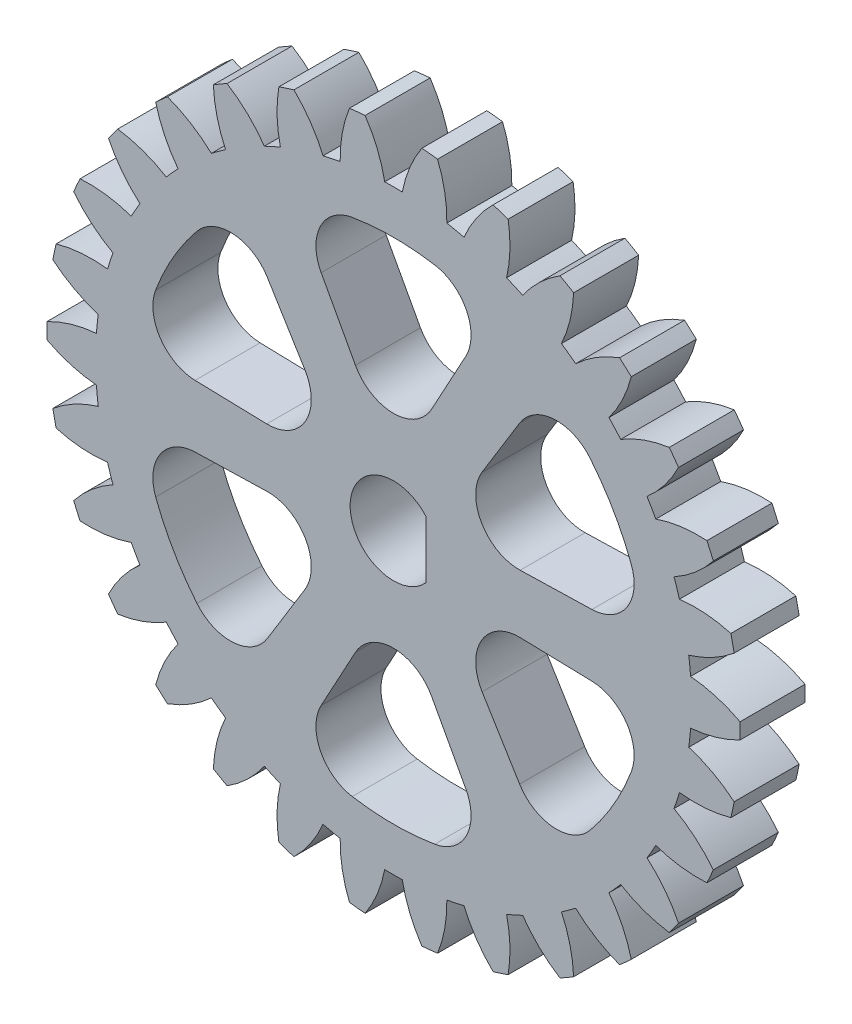
SolidWorks part; units mm, degrees
ref_plane "Front Plane" through (0, 0, 0) normal (0, 0, 1) x (1, 0, 0)
ref_plane "Top Plane" through (0, 0, 0) normal (0, 1, 0) x (1, 0, 0)
ref_plane "Right Plane" through (0, 0, 0) normal (1, 0, 0) x (0, 0, -1)
sketch "Sketch1" plane through (0, 0, 0) normal (0, 0, 1) x (1, 0, 0)
  circle A0 centre (0, 0) radius 16
  dimension "addendumDiameter" = 32
extrude "Boss-Extrude1" add sketch "Sketch1" along normal blind 3
sketch "Sketch3" plane through (0, 0, 3) normal (0, 0, 1) x (1, 0, 0)
  line L0 (0, 0) -> (-3.2905, 31.3074) construction
  line L1 (0, 0) -> (0, 28.4418) construction
  line L2 (-0.7847, 14.9795) -> (-1.5658, 14.8974) construction
  circle A0 centre (0, 0) radius 14.0954 construction
  circle A1 centre (0, 0) radius 15 construction
  circle A2 centre (0, 0) radius 13.75 construction
  arc A3 (0.4053, 13.744) -> (-0.4053, 13.744) centre (0, 0) ccw
  arc A4 (1.31, 15.9463) -> (-1.31, 15.9463) centre (0, 0) ccw
  circle A5 centre (0, 0) radius 16 construction
  arc A6 (-1.31, 15.9463) -> (-0.4053, 13.744) centre (-6.2972, 12.6105) cw
  arc A7 (1.31, 15.9463) -> (0.4053, 13.744) centre (6.2972, 12.6105) ccw
  point P16 (0, 13.75)
  dimension "D1" = 27.5
  dimension "D2" = 28.1908
  dimension "D3" = 30
  dimension "D5" = 6
  dimension "D6" = 6
  dimension "D4" = 6
  dimension "D7" = 0.7854
extrude "Cut-Extrude1" cut sketch "Sketch3" against normal through all
pattern_circular "CirPattern1" count 30 over 360 about axis through (0, 0, 0) along (0, 0, 1) of "Cut-Extrude1"
sketch "Sketch4" plane through (0, 0, 3) normal (0, 0, 1) x (1, 0, 0)
  line L0 (0, 0) -> (0, 11.7308) construction
  line L1 (0, 2.5) -> (-4.5201, 10.825)
  line L3 (4.5201, 10.825) -> (0, 2.5)
  arc A0 (-4.5201, 10.825) -> (4.5201, 10.825) centre (0, 0) cw
  point P7 (0, 11.7308)
  dimension "D1" = 2.5
  dimension "D2" = 9.2308
  dimension "D3" = 57
extrude "Cut-Extrude2" cut sketch "Sketch4" against normal through all
fillet "Fillet10" radius 2 3 edges at (-4.5201, 10.825, 1.5) (0, 2.5, 1.5) (4.5201, 10.825, 1.5)
pattern_circular "CirPattern2" count 6 over 360 about axis through (0, 0, 0) along (0, 0, 1) of "Fillet10", "Cut-Extrude2"
sketch "Sketch5" plane through (0, 0, 0) normal (0, 0, -1) x (-1, 0, 0)
  line L0 (-1.5, 1.3229) -> (-1.5, -1.3229)
  line L1 (0, 0) -> (-4.7764, 0) construction
  arc A0 (-1.5, 1.3229) -> (-1.5, -1.3229) centre (0, 0) cw
  dimension "D2" = 2
  dimension "D1" = 1.5
extrude "Cut-Extrude3" cut sketch "Sketch5" against normal through all
equation "\"module\"= 1.0"
equation "\"teeth\"= 30"
equation "\"pressureAngle\"= 20deg"
equation "\"gearThickness\"= 3"
equation "\"addendumFactor\"= 1"
equation "\"dedendumFactor\"= 1.25"
equation "\"pitch\"= 1 / \"module\""
equation "\"pitchDiameter\"= \"teeth\" / \"pitch\""
equation "\"addendum\"= \"addendumFactor\" / \"pitch\""
equation "\"dedendum\"= \"dedendumFactor\" / \"pitch\""
equation "\"addendumDiameter@Sketch1\"= \"pitchDiameter\" + 2 * \"addendum\""
equation "\"D1@Boss-Extrude1\"=\"gearThickness\""
equation "\"D1@Sketch3\"=\"pitchDiameter\" - 2 * \"dedendum\""
equation "\"D2@Sketch3\"=\"pitchDiameter\" * cos ( \"pressureAngle\" )"
equation "\"D3@Sketch3\"=\"pitchDiameter\""
equation "\"D5@Sketch3\"= \"pitchDiameter\" / 5"
equation "\"D6@Sketch3\"= \"pitchDiameter\" / 5"
equation "\"D4@Sketch3\"=180/\"teeth\""
equation "\"D1@CirPattern1\"=\"teeth\""
equation "\"D7@Sketch3\"= PI / 2 / \"pitch\" / 2"
equation "\"D1@Sketch4\"=\"pitchDiameter\"/12"
equation "\"D2@Sketch4\"=\"pitchDiameter\"/3.25"
